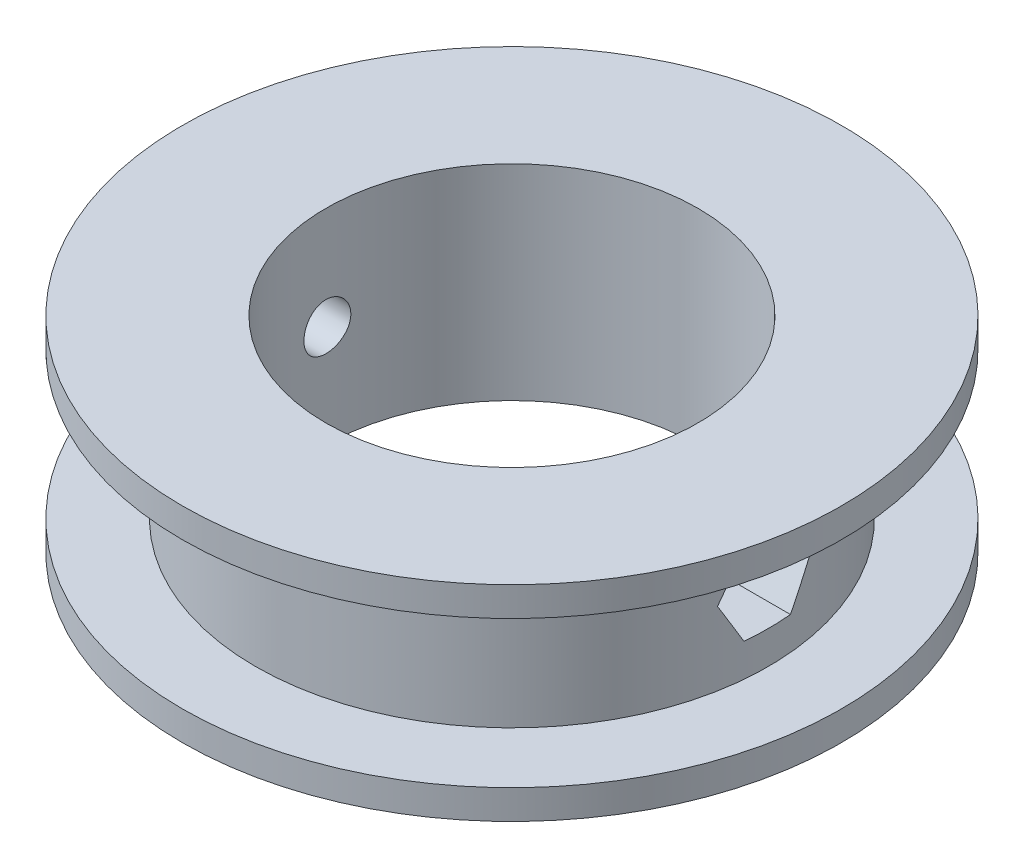
SolidWorks part; units mm, degrees
ref_plane "Front Plane" through (0, 0, 0) normal (0, 0, 1) x (1, 0, 0)
ref_plane "Top Plane" through (0, 0, 0) normal (0, 1, 0) x (1, 0, 0)
ref_plane "Right Plane" through (0, 0, 0) normal (1, 0, 0) x (0, 0, -1)
sketch "Sketch1" plane through (0, 0, 0) normal (0, 1, 0) x (1, 0, 0)
  circle A0 centre (0, 0) radius 12.7
  circle A1 centre (0, 0) radius 17.5
  dimension "D1" = 25.4
  dimension "D2" = 35
extrude "Boss-Extrude1" add sketch "Sketch1" along normal mid plane 10
sketch "Sketch2" plane through (0, 5, 0) normal (0, 1, 0) x (1, 0, 0)
  circle A0 centre (0, 0) radius 12.7 construction
  circle A1 centre (0, 0) radius 22.5
  circle A3 centre (0, 0) radius 12.7
  circle A4 centre (0, 0) radius 17.5 construction
  dimension "D1" = 5
extrude "Boss-Extrude2" add sketch "Sketch2" along normal blind 2
mirror "Mirror1" about plane through (0, 0, 0) normal (0, 1, 0) of "Boss-Extrude2"
sketch "Sketch3" plane through (0, 0, 0) normal (1, 0, 0) x (0, 0, -1)
  circle A0 centre (0, 0) radius 1.6
extrude "Cut-Extrude1" cut sketch "Sketch3" against normal through all
sketch "Sketch4" plane through (0, 0, 0) normal (1, 0, 0) x (0, 0, -1)
  line L1 (3.1754, 0) -> (1.5877, 2.75)
  line L2 (1.5877, 2.75) -> (-1.5877, 2.75)
  line L3 (-1.5877, 2.75) -> (-3.1754, 0)
  line L4 (-3.1754, 0) -> (-1.5877, -2.75)
  line L5 (-1.5877, -2.75) -> (1.5877, -2.75)
  line L6 (1.5877, -2.75) -> (3.1754, 0)
  circle A0 centre (0, 0) radius 2.75 construction
  point P1 (0, 2.75)
  dimension "D1" = 5.5
extrude "Cut-Extrude2" cut sketch "Sketch4" along normal through all
ref_plane "Plane1" through (-15, 0, 0) normal (1, 0, 0) x (0, 0, -1)
sketch "Sketch5" plane through (-15, 0, 0) normal (1, 0, 0) x (0, 0, -1)
  circle A0 centre (0, 0) radius 2.75
  dimension "D1" = 5.5
extrude "Cut-Extrude3" cut sketch "Sketch5" against normal through all
